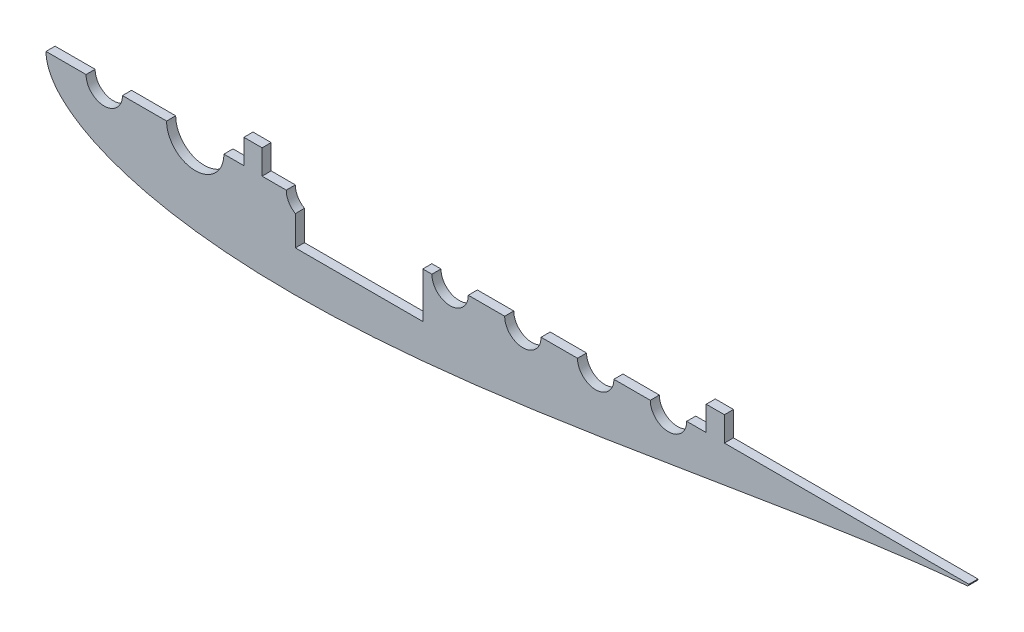
SolidWorks part; units mm, degrees
ref_plane "Front Plane" through (0, 0, 0) normal (0, 0, 1) x (1, 0, 0)
ref_plane "Top Plane" through (0, 0, 0) normal (0, 1, 0) x (1, 0, 0)
ref_plane "Right Plane" through (0, 0, 0) normal (1, 0, 0) x (0, 0, -1)
curve "Curve4"
  spline degree 3 poles (100, 0, 0) (99.8498, 0.0023, 0) (99.4759, 0.008, 0) (99.1023, 0.0238, 0) (98.8789, 0.0332, 0) knots 0 0 0 0 0.401829 1 1 1 1
curve "Curve5"
  spline degree 3 poles (99.3714, -0.0082, 0) (100.2526, 0, 0) (99.3714, 0.0082, 0) (98.8504, 0.035, 0) (97.904, 0.0811, 0) (96.8285, 0.1543, 0) (95.5159, 0.2583, 0) (94.013, 0.3972, 0) (92.313, 0.574, 0) (90.4281, 0.791, 0) (88.3655, 1.0495, 0) (86.1348, 1.3497, 0) (83.7456, 1.691, 0) (81.2082, 2.0715, 0) (78.5335, 2.4886, 0) (75.7326, 2.9386, 0) (72.8172, 3.4168, 0) (69.799, 3.9177, 0) (66.6904, 4.435, 0) (63.5039, 4.9616, 0) (60.2521, 5.4899, 0) (56.948, 6.0119, 0) (53.6049, 6.519, 0) (50.2363, 7.0024, 0) (46.8558, 7.4534, 0) (43.4774, 7.8632, 0) (40.1152, 8.2232, 0) (36.7837, 8.5249, 0) (33.4975, 8.7606, 0) (30.2716, 8.923, 0) (27.1211, 9.0055, 0) (24.0614, 9.0025, 0) (21.108, 8.909, 0) (18.277, 8.7213, 0) (15.5843, 8.4369, 0) (13.0466, 8.0543, 0) (10.6806, 7.5735, 0) (8.5039, 6.996, 0) (6.5349, 6.3253, 0) (4.7933, 5.5673, 0) (3.3001, 4.7321, 0) (2.0777, 3.8366, 0) (1.1467, 2.91, 0) (0.5165, 2.0014, 0) (0.165, 1.1816, 0) (0.0231, 0.524, 0) (-0.0093, 0, 0) (0.0231, -0.524, 0) (0.165, -1.1816, 0) (0.5165, -2.0014, 0) (1.1467, -2.91, 0) (2.0777, -3.8366, 0) (3.3001, -4.7321, 0) (4.7933, -5.5673, 0) (6.5349, -6.3253, 0) (8.5039, -6.996, 0) (10.6806, -7.5735, 0) (13.0466, -8.0543, 0) (15.5843, -8.4369, 0) (18.277, -8.7213, 0) (21.108, -8.909, 0) (24.0614, -9.0025, 0) (27.1211, -9.0055, 0) (30.2716, -8.923, 0) (33.4975, -8.7606, 0) (36.7837, -8.5249, 0) (40.1152, -8.2232, 0) (43.4774, -7.8632, 0) (46.8558, -7.4534, 0) (50.2363, -7.0024, 0) (53.6049, -6.519, 0) (56.948, -6.0119, 0) (60.2521, -5.4899, 0) (63.5039, -4.9616, 0) (66.6904, -4.435, 0) (69.799, -3.9177, 0) (72.8172, -3.4168, 0) (75.7326, -2.9386, 0) (78.5335, -2.4886, 0) (81.2082, -2.0715, 0) (83.7456, -1.691, 0) (86.1348, -1.3497, 0) (88.3655, -1.0495, 0) (90.4281, -0.791, 0) (92.313, -0.574, 0) (94.013, -0.3972, 0) (95.5159, -0.2583, 0) (96.8285, -0.1543, 0) (97.904, -0.0811, 0) (98.8504, -0.035, 0) (99.3714, -0.0082, 0) (100.2526, 0, 0) (99.3714, 0.0082, 0) knots -0.009667 -0.005395 -0.002168 0 0.002168 0.005395 0.009667 0.014967 0.021271 0.028553 0.036781 0.04592 0.055932 0.066773 0.078397 0.090755 0.103793 0.117456 0.131686 0.146422 0.1616 0.177156 0.193024 0.209135 0.225421 0.241812 0.258238 0.274629 0.290914 0.307025 0.322893 0.338448 0.353626 0.368361 0.38259 0.396253 0.40929 0.421647 0.43327 0.444109 0.454119 0.463255 0.471479 0.478755 0.485052 0.490344 0.49461 0.497833 0.5 0.502167 0.50539 0.509656 0.514948 0.521245 0.528521 0.536745 0.545881 0.555891 0.56673 0.578353 0.59071 0.603747 0.61741 0.631639 0.646374 0.661552 0.677107 0.692975 0.709086 0.725371 0.741762 0.758188 0.774579 0.790865 0.806976 0.822844 0.8384 0.853578 0.868314 0.882544 0.896207 0.909245 0.921603 0.933227 0.944068 0.95408 0.963219 0.971447 0.978729 0.985033 0.990333 0.994605 0.997832 1 1.002168 1.005395 1.009667 periodic
sketch "Sketch2" plane through (0, 0, 0) normal (0, 0, 1) x (1, 0, 0)
  line L0 (100, 0) -> (0, 0) construction
  line L1 (1.2169, -991.9959) -> (1.2169, 49008.0041) construction
  line L2 (84.14, 0) -> (124.14, 0) construction
  line L3 (125.634, 0) -> (131.6629, 0) construction
  line L4 (180.34, 0) -> (231.14, 0) construction
  line L9 (0, 0) -> (643.9668, 0)
  line L12 (150.781, 0) -> (150.781, 17.145)
  line L13 (460.661, 0) -> (473.361, 0)
  line L14 (460.661, 0) -> (460.661, 17.145)
  line L15 (460.661, 17.145) -> (473.361, 17.145)
  line L16 (473.361, 0) -> (473.361, 17.145)
  line L18 (138.081, 0) -> (138.081, 17.145)
  line L19 (138.081, 17.145) -> (150.781, 17.145)
  line L20 (173.99, 31.75) -> (262.89, 31.75)
  line L21 (173.99, 31.75) -> (173.99, -31.75)
  line L22 (173.99, -31.75) -> (262.89, -31.75)
  line L23 (262.89, 31.75) -> (262.89, -31.75)
  line L24 (173.99, 31.75) -> (262.89, -31.75) construction
  line L25 (173.99, -31.75) -> (262.89, 31.75) construction
  circle A0 centre (104.14, 0) radius 20 construction
  arc A1 (1.2169, -4.6585) -> (1.2169, 4.6585) centre (9.525, 0) cw
  circle A2 centre (180.34, 0) radius 12.7
  circle A3 centre (231.14, 0) radius 12.7
  circle A4 centre (104.14, 0) radius 20
  circle A5 centre (281.94, 0) radius 12.7
  circle A6 centre (332.74, 0) radius 12.7
  circle A7 centre (383.54, 0) radius 12.7
  circle A8 centre (434.34, 0) radius 12.7
  circle A9 centre (40.64, 0) radius 12.7
  circle A14 centre (642.3793, 0) radius 1.5875 construction
  arc A15 (642.5108, -1.582) -> (642.5108, 1.582) centre (642.3793, 0) ccw
  spline S2 degree 3 poles (666.3448, -0.0547) (672.2538, 0) (666.3448, 0.0547) (662.8509, 0.2344) (656.505, 0.5436) (649.293, 1.0348) (640.4916, 1.7319) (630.4138, 2.6634) (619.0141, 3.8493) (606.375, 5.3044) (592.5439, 7.0376) (577.5855, 9.0506) (561.5643, 11.3389) (544.5497, 13.8907) (526.6141, 16.6877) (507.8326, 19.7051) (488.2827, 22.9117) (468.0444, 26.2704) (447.1994, 29.739) (425.8316, 33.2703) (404.0263, 36.8132) (381.8707, 40.3133) (359.4533, 43.7135) (336.8645, 46.9554) (314.1962, 49.9798) (291.5418, 52.7277) (268.9963, 55.1412) (246.6566, 57.1646) (224.6209, 58.7452) (202.9892, 59.8341) (181.8631, 60.3875) (161.3458, 60.367) (141.542, 59.7399) (122.5581, 58.4818) (104.5023, 56.5743) (87.485, 54.0089) (71.6197, 50.7848) (57.0237, 46.9125) (43.8205, 42.415) (32.1416, 37.3322) (22.1291, 31.7315) (13.9324, 25.7264) (7.6896, 19.5132) (3.4631, 13.4204) (1.1063, 7.9234) (0.1546, 3.5138) (-0.0622, 0) (0.1546, -3.5138) (1.1063, -7.9234) (3.4631, -13.4204) (7.6896, -19.5132) (13.9324, -25.7264) (22.1291, -31.7315) (32.1416, -37.3322) (43.8205, -42.415) (57.0237, -46.9125) (71.6197, -50.7848) (87.485, -54.0089) (104.5023, -56.5743) (122.5581, -58.4818) (141.542, -59.7399) (161.3458, -60.367) (181.8631, -60.3875) (202.9892, -59.8341) (224.6209, -58.7452) (246.6566, -57.1646) (268.9963, -55.1412) (291.5418, -52.7277) (314.1962, -49.9798) (336.8645, -46.9554) (359.4533, -43.7135) (381.8707, -40.3133) (404.0263, -36.8132) (425.8316, -33.2703) (447.1994, -29.739) (468.0444, -26.2704) (488.2827, -22.9117) (507.8326, -19.7051) (526.6141, -16.6877) (544.5497, -13.8907) (561.5643, -11.3389) (577.5855, -9.0506) (592.5439, -7.0376) (606.375, -5.3044) (619.0141, -3.8493) (630.4138, -2.6634) (640.4916, -1.7319) (649.293, -1.0348) (656.505, -0.5436) (662.8509, -0.2344) (666.3448, -0.0547) (672.2538, 0) (666.3448, 0.0547) knots -0.009667 -0.005395 -0.002168 0 0.002168 0.005395 0.009667 0.014967 0.021271 0.028553 0.036781 0.04592 0.055932 0.066773 0.078397 0.090755 0.103793 0.117456 0.131686 0.146422 0.1616 0.177156 0.193024 0.209135 0.225421 0.241812 0.258238 0.274629 0.290914 0.307025 0.322893 0.338448 0.353626 0.368361 0.38259 0.396253 0.40929 0.421647 0.43327 0.444109 0.454119 0.463255 0.471479 0.478755 0.485052 0.490344 0.49461 0.497833 0.5 0.502167 0.50539 0.509656 0.514948 0.521245 0.528521 0.536745 0.545881 0.555891 0.56673 0.578353 0.59071 0.603747 0.61741 0.631639 0.646374 0.661552 0.677107 0.692975 0.709086 0.725371 0.741762 0.758188 0.774579 0.790865 0.806976 0.822844 0.8384 0.853578 0.868314 0.882544 0.896207 0.909245 0.921603 0.933227 0.944068 0.95408 0.963219 0.971447 0.978729 0.985033 0.990333 0.994605 0.997832 1 1.002168 1.005395 1.009667 only from (670.56, 0) to (670.56, 0)
  point P2 (167.64, 0)
  point P8 (1.2169, -4.6585)
  point P10 (1.2169, 4.6585)
  point P28 (133.9182, 0)
  point P45 (218.44, 0)
  point P49 (130.0977, 0)
  point P59 (95.1064, 0)
  dimension "D2" = 40
  dimension "D3" = 25.4
  dimension "D11" = 12.7
  dimension "D4" = 76.2
  dimension "D5" = 6
  dimension "D7" = 50.8
  dimension "D8" = 25.4
  dimension "D9" = 63.5
  dimension "D10" = 3.175
  dimension "D1" = 167.64
  dimension "D6" = 63.5
  dimension "D12" = 17.145
  dimension "D13" = 2
  dimension "D14" = 88.9
  dimension "D15" = 63.5
  dimension "D16" = 69.85
extrude "Boss-Extrude1" add sketch "Sketch2" along normal blind 6.35
equation "\"0.5n\"=0"
